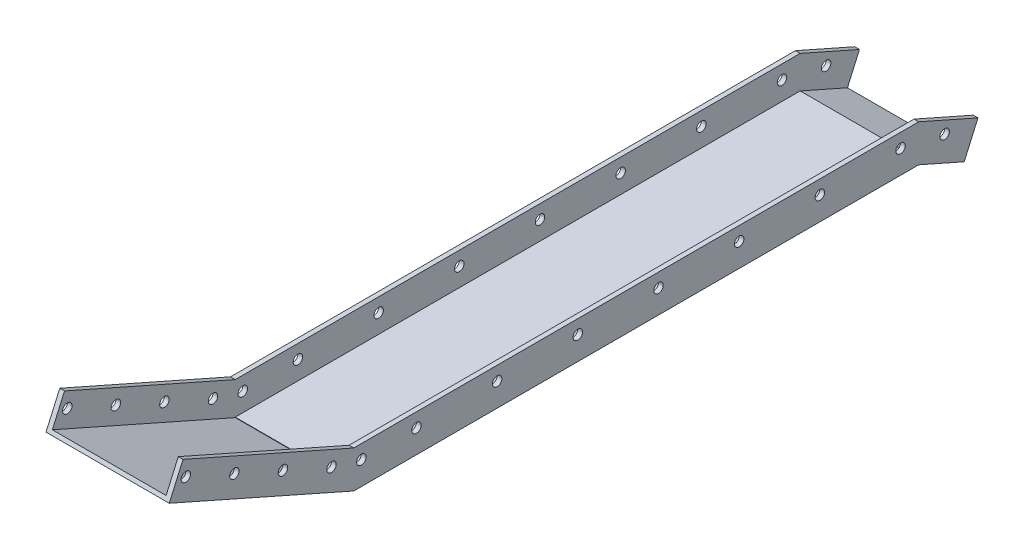
SolidWorks part; units mm, degrees
ref_plane "Front Plane" through (0, 0, 0) normal (0, 0, 1) x (1, 0, 0)
ref_plane "Top Plane" through (0, 0, 0) normal (0, 1, 0) x (1, 0, 0)
ref_plane "Right Plane" through (0, 0, 0) normal (1, 0, 0) x (0, 0, -1)
sketch "Sketch1" plane through (0, 0, 0) normal (1, 0, 0) x (0, 0, -1)
  line L1 (-297.9495, 14.65) -> (297.9495, 14.65)
  line L2 (-297.9495, 14.65) -> (-297.9495, -14.65)
  line L3 (-297.9495, -14.65) -> (297.9495, -14.65)
  line L4 (297.9495, 14.65) -> (297.9495, -14.65)
  line L5 (-297.9495, 14.65) -> (297.9495, -14.65) construction
  line L6 (-297.9495, -14.65) -> (297.9495, 14.65) construction
  point P0 (0, 0)
  dimension "D1" = 595.899
  dimension "D2" = 29.3
extrude "Boss-Extrude1" add sketch "Sketch1" against normal blind 10
ref_plane "Plane1" through (-70, 0, 0) normal (-1, 0, 0) x (0, 0, 1)
sketch "Sketch2" plane through (0, -14.65, 0) normal (0, -1, 0) x (1, 0, 0)
  line L5 (0, 297.9495) -> (-140, 297.9495)
  line L6 (0, 297.9495) -> (0, -297.9495)
  line L7 (0, -297.9495) -> (-140, -297.9495)
  line L8 (-140, 297.9495) -> (-140, -297.9495)
  dimension "D1" = 140
  dimension "D2" = 595.899
extrude "Boss-Extrude2" add sketch "Sketch2" along normal blind 10
sketch "Sketch4" plane through (-10, 0, 0) normal (-1, 0, 0) x (0, 0, 1)
  line L0 (-297.9495, 0) -> (-278.7995, 0) construction
  line L1 (-297.9495, -14.65) -> (-297.9495, 14.65) construction
  line L2 (231.8005, 0) -> (297.9495, 0) construction
  line L3 (297.9495, 14.65) -> (297.9495, -24.65) construction
  circle A1 centre (-278.7995, 0) radius 5
  circle A2 centre (-193.6995, 0) radius 5
  circle A3 centre (-108.5995, 0) radius 5
  circle A4 centre (-23.4995, 0) radius 5
  circle A5 centre (61.6005, 0) radius 5
  circle A6 centre (146.7005, 0) radius 5
  circle A7 centre (231.8005, 0) radius 5
  circle A13 centre (289.9495, 0) radius 5
  dimension "D2" = 10
  dimension "D1" = 19.15
  dimension "D3" = 7
mirror "Mirror2" about plane through (-70, 0, 0) normal (-1, 0, 0) of "Boss-Extrude1"
ref_plane "Plane2" through (-10, 14.65, -297.9495) normal (0, 1, 0) x (1, 0, 0)
extrude "Cut-Extrude1" cut sketch "Sketch4" along normal mid plane 2000
sketch "Sketch7" plane through (-140, 0, 0) normal (-1, 0, 0) x (0, 0, 1)
  line L0 (297.9495, -24.65) -> (492.5601, 61.4271)
  line L1 (297.9495, -24.65) -> (297.9495, 14.65) construction
  line L2 (297.9495, 14.65) -> (478.0218, 94.2967)
  line L3 (492.5601, 61.4271) -> (478.0218, 94.2967)
  line L4 (297.9495, -24.65) -> (297.9495, 14.65)
  dimension "D1" = 66.14
  dimension "D2" = 196.9
extrude "Boss-Extrude5" add sketch "Sketch7" against normal up to surface (10 mm away) up to face at (-130, 0, -273.7995)
sketch "Sketch8" plane through (0, 0, 0) normal (1, 0, 0) x (0, 0, -1)
  line L0 (-297.9495, 14.65) -> (-478.0218, 94.2967)
  line L1 (-478.0218, 94.2967) -> (-492.5601, 61.4271)
  line L2 (-492.5601, 61.4271) -> (-297.9495, -24.65)
  line L3 (-297.9495, -24.65) -> (-297.9495, 14.65)
extrude "Boss-Extrude6" add sketch "Sketch8" along direction (1, 0, 0) on the side against the normal up to surface (10 mm away)
sketch "Sketch9" plane through (0, 192.2651, 434.6899) normal (0, 0.4045, 0.9145) x (1, 0, 0)
  line L1 (-130, -133.9195) -> (-10, -133.9195)
  line L2 (-130, -133.9195) -> (-130, -143.0649)
  line L3 (-130, -143.0649) -> (-10, -143.0649)
  line L4 (-10, -133.9195) -> (-10, -143.0649)
extrude "Boss-Extrude7" add sketch "Sketch9" against normal up to surface (208.7519 mm away)
sketch "Sketch18" plane through (0, 0, -297.9495) normal (0, 0, -1) x (-1, 0, 0)
  line L1 (10, -14.65) -> (130, -14.65)
  line L2 (10, -14.65) -> (10, -19.65)
  line L3 (10, -19.65) -> (130, -19.65)
  line L4 (130, -14.65) -> (130, -19.65)
  dimension "D1" = 5
extrude "Cut-Extrude4" cut sketch "Sketch18" against normal up to vertex (595.899 mm away)
sketch "Sketch10" plane through (-140, 0, 0) normal (-1, 0, 0) x (0, 0, 1)
  line L0 (-297.9495, -24.65) -> (-345.9627, -45.8864)
  line L2 (-297.9495, 14.65) -> (-360.501, -13.0168)
  line L4 (-297.9495, 14.65) -> (-297.9495, -24.65)
  line L5 (-360.501, -13.0168) -> (-345.9627, -45.8864)
  line L7 (297.9495, -24.65) -> (-297.9495, -24.65) construction
  dimension "D1" = 156.14
  dimension "D2" = 52.5
extrude "Boss-Extrude8" add sketch "Sketch10" against normal up to surface (10 mm away)
sketch "Sketch11" plane through (0, 0, 0) normal (1, 0, 0) x (0, 0, -1)
  line L0 (297.9495, -24.65) -> (345.9627, -45.8864)
  line L3 (297.9495, 14.65) -> (297.9495, -24.65)
  line L6 (297.9495, 14.65) -> (360.501, -13.0168)
  line L7 (345.9627, -45.8864) -> (360.501, -13.0168)
extrude "Boss-Extrude9" add sketch "Sketch11" against normal up to surface (10 mm away) up to face at (-10, 0, -283.7995)
sketch "Sketch14" plane through (-130, 0, 0) normal (1, 0, 0) x (0, 0, -1)
  line L0 (297.9495, -24.65) -> (345.9627, -45.8864)
  line L5 (297.9495, -19.65) -> (297.9495, -24.65)
  line L14 (345.9627, -45.8864) -> (347.8123, -41.7045)
  line L17 (297.9495, -19.65) -> (347.8123, -41.7045)
extrude "Boss-Extrude11" add sketch "Sketch14" along normal up to surface (120 mm away) up to face at (-10, 0, -283.7995)
sketch "Sketch15" plane through (-140, 0, 0) normal (-1, 0, 0) x (0, 0, 1)
  line L0 (231.8005, 0) -> (231.8005, 14.65) construction
  line L1 (297.9495, -24.65) -> (323.7999, -24.65) construction
  line L2 (297.9495, -24.65) -> (297.9495, 14.65) construction
  line L3 (-297.9495, 14.65) -> (297.9495, 14.65) construction
  line L4 (321.4091, 8.9525) -> (372.6231, 31.6047) construction
  line L6 (478.0218, 94.2967) -> (297.9495, 14.65) construction
  line L7 (315.4629, 22.3962) -> (321.4091, 8.9525) construction
  line L8 (297.9495, 14.65) -> (315.4629, 22.3962) construction
  circle A0 centre (321.4091, 8.9525) radius 5
  circle A5 centre (372.6231, 31.6047) radius 5
  circle A6 centre (423.8372, 54.2569) radius 5
  circle A7 centre (475.0512, 76.9091) radius 5
  dimension "D3" = 10
  dimension "D1" = 14.7
  dimension "D2" = 19.15
  dimension "D4" = 4
  dimension "D5" = 56
extrude "Cut-Extrude2" cut sketch "Sketch15" against normal blind 200
sketch "Sketch16" plane through (-140, 0, 0) normal (-1, 0, 0) x (0, 0, 1)
  line L0 (-297.9495, -24.65) -> (-315.5086, -32.4165) construction
  line L1 (-345.9627, -45.8864) -> (-297.9495, -24.65) construction
  line L2 (-315.5086, -32.4165) -> (-325.2976, -10.2847) construction
  circle A0 centre (-325.2976, -10.2847) radius 5
  dimension "D3" = 10
  dimension "D1" = 19.2
  dimension "D2" = 24.2
  dimension "D5" = 270
extrude "Cut-Extrude3" cut sketch "Sketch16" against normal blind 200
sketch "Sketch17" plane through (-140, 0, 0) normal (-1, 0, 0) x (0, 0, 1)
  line L0 (-297.9495, -24.65) -> (-200.4468, -245.0927) construction
  line L2 (297.9495, -24.65) -> (-200.4468, -245.0927) construction
  line L3 (-360.501, -13.0168) -> (-345.9627, -45.8864) construction
  dimension "D1" = 241.0431
  dimension "D2" = 544.9714
sketch "Sketch19" plane through (0, 0, 297.9495) normal (0, 0, -1) x (-1, 0, 0)
  line L1 (10, -14.65) -> (130, -14.65)
  line L2 (10, -14.65) -> (10, -19.65)
  line L3 (10, -19.65) -> (130, -19.65)
  line L4 (130, -14.65) -> (130, -19.65)
sketch "Sketch21" plane through (0, 192.2651, 434.6899) normal (0, 0.4045, 0.9145) x (1, 0, 0)
  line L1 (-130, -133.9195) -> (-10, -133.9195)
  line L2 (-130, -133.9195) -> (-130, -138.9195)
  line L3 (-130, -138.9195) -> (-10, -138.9195)
  line L4 (-10, -133.9195) -> (-10, -138.9195)
  dimension "D1" = 5
extrude "Cut-Extrude5" cut sketch "Sketch21" against normal up to surface (208.7519 mm away)
sketch "Sketch23" plane through (0, 14.65, 0) normal (0, 1, 0) x (1, 0, 0)
  line L0 (-130, 297.9495) -> (-140, 297.9495) construction
  line L2 (-140, -297.9495) -> (-140, 297.9495)
  line L4 (-135, -297.9495) -> (-135, 297.9495)
  line L7 (-135, 297.9495) -> (-135, 372.2393)
  line L8 (-135, 372.2393) -> (-140, 372.2393)
  line L9 (-140, 297.9495) -> (-140, 372.2393)
  line L11 (-135, -297.9495) -> (-135, -501.7969)
  line L12 (-135, -501.7969) -> (-140, -501.7969)
  line L13 (-140, -297.9495) -> (-140, -501.7969)
extrude "Cut-Extrude6" cut sketch "Sketch23" against normal mid plane 1000
mirror "Mirror3" about plane through (-70, 0, 0) normal (-1, 0, 0) of "Cut-Extrude6"
